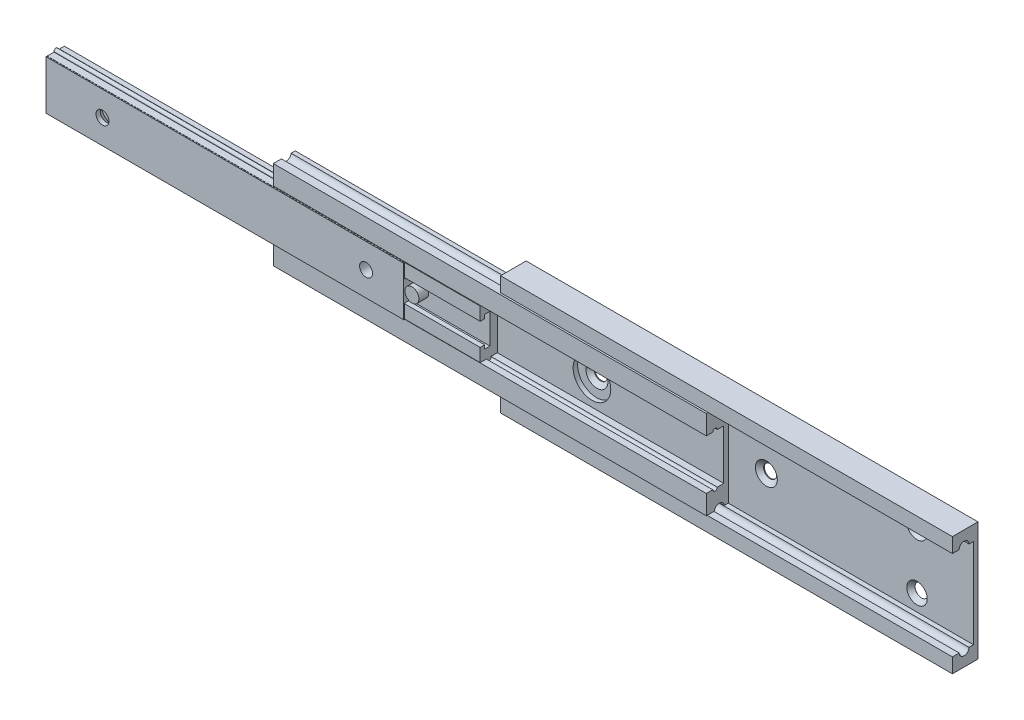
SolidWorks part; units mm, degrees
ref_plane "Front" through (0, 0, 0) normal (0, 0, 1) x (1, 0, 0)
ref_plane "Top" through (0, 0, 0) normal (0, 1, 0) x (1, 0, 0)
ref_plane "Right" through (0, 0, 0) normal (1, 0, 0) x (0, 0, -1)
sketch "Sketch1" plane through (0, 0, 0) normal (1, 0, 0) x (0, 0, -1)
  line L0 (-4.318, -20.0422) -> (4.318, 20.0422) construction
  line L1 (-4.318, 20.0422) -> (4.318, 20.0422)
  line L2 (-4.318, 20.0422) -> (-4.318, 15.0892)
  line L3 (-4.318, -20.0422) -> (4.318, -20.0422)
  line L4 (4.318, 20.0422) -> (4.318, -20.0422)
  line L5 (2.794, 15.0892) -> (2.794, -15.0892)
  line L6 (2.794, 15.0892) -> (1.27, 15.0892)
  line L7 (2.794, -15.0892) -> (1.27, -15.0892)
  line L8 (-4.318, -15.0892) -> (-4.318, -20.0422)
  line L9 (-2.032, 15.0892) -> (-4.318, 15.0892)
  line L10 (-2.032, -15.0892) -> (-4.318, -15.0892)
  arc A0 (1.27, 15.0892) -> (-2.032, 15.0892) centre (-0.381, 15.0892) ccw
  arc A1 (-2.032, -15.0892) -> (1.27, -15.0892) centre (-0.381, -15.0892) ccw
  dimension "D5" = 3.302
  dimension "D1" = 40.0844
  dimension "D2" = 8.636
  dimension "D3" = 1.524
  dimension "D4" = 4.953
  dimension "D6" = 3.175
extrude "Extrude1" add sketch "Sketch1" along normal blind 152.4
ref_plane "Plane1" through (-76.2, 0, 0) normal (1, 0, 0) x (0, 0, -1)
sketch "Sketch2" plane through (-76.2, 0, 0) normal (1, 0, 0) x (0, 0, -1)
  line L0 (2.794, 15.0892) -> (2.794, -15.0892) construction
  line L1 (-4.7625, 14.9368) -> (-2.025, 14.9368)
  line L2 (-4.7625, 14.9368) -> (-4.7625, 8.4074)
  line L3 (-4.7625, -14.9368) -> (-2.025, -14.9368)
  line L4 (2.6416, 14.9368) -> (2.6416, -14.9368)
  line L5 (-4.318, 15.0892) -> (-2.032, 15.0892) construction
  line L6 (4.318, -20.0422) -> (4.318, 20.0422) construction
  line L7 (-2.032, -15.0892) -> (-4.318, -15.0892) construction
  line L8 (1.263, -14.9368) -> (2.6416, -14.9368)
  line L9 (1.263, 14.9368) -> (2.6416, 14.9368)
  line L10 (-4.7625, 8.4074) -> (-2.5844, 8.4074)
  line L11 (-3.6068, 8.255) -> (0.9652, 8.255) construction
  line L12 (-3.6068, 8.255) -> (-3.6068, -8.255) construction
  line L13 (-3.6068, -8.255) -> (0.9652, -8.255) construction
  line L14 (0.9652, 8.255) -> (0.9652, -8.255) construction
  line L15 (1.1176, 8.4074) -> (1.1176, -8.4074)
  line L16 (1.1176, -8.4074) -> (-1.0604, -8.4074)
  line L17 (-4.7625, -8.4074) -> (-4.7625, -14.9368)
  line L18 (-1.0604, 8.4074) -> (1.1176, 8.4074)
  line L19 (-4.7625, 8.4074) -> (1.1176, 8.4074) construction
  line L20 (-2.5844, -8.4074) -> (-4.7625, -8.4074)
  arc A0 (-2.025, 14.9368) -> (1.263, 14.9368) centre (-0.381, 15.0892) ccw
  arc A1 (1.27, 15.0892) -> (-2.032, 15.0892) centre (-0.381, 15.0892) ccw construction
  arc A2 (1.263, -14.9368) -> (-2.025, -14.9368) centre (-0.381, -15.0892) ccw
  arc A3 (-2.032, -15.0892) -> (1.27, -15.0892) centre (-0.381, -15.0892) ccw construction
  arc A4 (-1.0604, 8.4074) -> (-2.5844, 8.4074) centre (-1.8224, 8.4074) ccw
  arc A5 (-2.5844, -8.4074) -> (-1.0604, -8.4074) centre (-1.8224, -8.4074) ccw
  point P28 (0.9652, 0)
  dimension "D11" = 1.524
  dimension "D1" = 0.1524
  dimension "D2" = 0.1524
  dimension "D3" = 9.0805
  dimension "D4" = 0.1524
  dimension "D5" = 16.51
  dimension "D6" = 7.9248
  dimension "D7" = 4.572
  dimension "D8" = 0.1524
  dimension "D9" = 0.1524
  dimension "D10" = 0.1524
extrude "Extrude2" add sketch "Sketch2" along normal blind 146.05
ref_plane "Plane2" through (-152.4, 0, 0) normal (1, 0, 0) x (0, 0, -1)
sketch "Sketch3" plane through (-152.4, 0, 0) normal (1, 0, 0) x (0, 0, -1)
  line L0 (4.318, -20.0422) -> (4.318, 20.0422) construction
  line L1 (-4.826, 8.255) -> (-2.5209, 8.255)
  line L2 (-4.826, 8.255) -> (-4.826, 3.81)
  line L3 (-4.826, -8.255) -> (-2.5209, -8.255)
  line L4 (0.9652, 8.255) -> (0.9652, -8.255)
  line L5 (-4.7625, 8.4074) -> (-2.5844, 8.4074) construction
  line L6 (1.1176, 8.4074) -> (1.1176, -8.4074) construction
  line L7 (-1.1239, 8.255) -> (0.9652, 8.255)
  line L8 (-2.5209, 8.4074) -> (-2.5209, 8.255)
  line L9 (-1.1239, 8.4074) -> (-1.1239, 8.255)
  line L10 (-2.5209, -8.4074) -> (-2.5209, -8.255)
  line L11 (-1.1239, -8.4074) -> (-1.1239, -8.255)
  line L12 (-1.1239, -8.255) -> (0.9652, -8.255)
  line L13 (-4.826, 8.255) -> (-4.7625, 8.4074) construction
  line L14 (-4.7625, -8.4074) -> (-4.826, -8.255) construction
  line L15 (-4.826, 3.81) -> (-3.302, 3.81)
  line L16 (-3.302, 3.81) -> (-3.302, 5.08)
  line L17 (-3.302, 5.08) -> (-1.524, 5.08)
  line L18 (-4.826, -3.81) -> (-4.826, -8.255)
  line L19 (-1.524, 5.08) -> (-1.524, -5.08)
  line L20 (-1.524, -5.08) -> (-3.302, -5.08)
  line L21 (-3.302, -5.08) -> (-3.302, -3.81)
  line L22 (-3.302, -3.81) -> (-4.826, -3.81)
  arc A0 (-1.1239, 8.4074) -> (-2.5209, 8.4074) centre (-1.8224, 8.4074) ccw
  arc A3 (-1.0604, 8.4074) -> (-2.5844, 8.4074) centre (-1.8224, 8.4074) ccw construction
  arc A4 (-2.5209, -8.4074) -> (-1.1239, -8.4074) centre (-1.8224, -8.4074) ccw
  arc A5 (-2.5844, -8.4074) -> (-1.0604, -8.4074) centre (-1.8224, -8.4074) ccw construction
  dimension "D5" = 1.397
  dimension "D1" = 7.62
  dimension "D2" = 9.144
  dimension "D3" = 0.1524
  dimension "D4" = 0.1524
  dimension "D6" = 10.16
  dimension "D7" = 1.778
  dimension "D8" = 1.524
extrude "Extrude3" add sketch "Sketch3" along normal blind 146.05
sketch "Sketch9" plane through (0, 0, 1.524) normal (0, 0, 1) x (1, 0, 0)
  line L0 (-6.35, 5.08) -> (-6.35, -5.08) construction
  circle A0 centre (-29.3751, 0) radius 2.3749
  dimension "D2" = 4.7498
  dimension "D1" = 25.4
extrude "Extrude4" add sketch "Sketch9" along normal up to surface (3.302 mm away) up to face at (-79.375, 6.0325, 4.826)
sketch "Sketch10" plane through (-152.4, 0, 0) normal (1, 0, 0) x (0, 0, -1)
  line L0 (-4.8768, 8.255) -> (-4.8768, 3.556)
  line L1 (-4.8768, 3.556) -> (-3.048, 3.556)
  line L2 (-3.048, 3.556) -> (-3.048, 4.826)
  line L3 (-3.048, 4.826) -> (-1.778, 4.826)
  line L4 (-1.778, 4.826) -> (-1.778, -4.826)
  line L5 (-1.778, -4.826) -> (-3.048, -4.826)
  line L6 (-3.048, -4.826) -> (-3.048, -3.556)
  line L7 (-3.048, -3.556) -> (-4.8768, -3.556)
  line L8 (-4.8768, -3.556) -> (-4.8768, -8.255)
  line L9 (-4.8768, -8.255) -> (-5.207, -8.255)
  line L10 (-5.207, -8.255) -> (-5.207, 8.255)
  line L11 (-5.207, 8.255) -> (-4.8768, 8.255)
  line L12 (-1.778, 0) -> (-5.207, 0) construction
  line L13 (4.318, -20.0422) -> (4.318, 20.0422) construction
  line L14 (-4.826, 8.255) -> (-4.826, 3.81) construction
  line L15 (-4.826, 3.81) -> (-3.302, 3.81) construction
  line L16 (-3.302, 3.81) -> (-3.302, 5.08) construction
  line L17 (-1.524, 5.08) -> (-1.524, -5.08) construction
  line L18 (-3.302, 5.08) -> (-1.524, 5.08) construction
  dimension "D1" = 16.51
  dimension "D2" = 9.525
  dimension "D3" = 0.0508
  dimension "D4" = 0.254
  dimension "D5" = 0.254
  dimension "D6" = 0.254
  dimension "D7" = 0.254
extrude "Extrude5" add sketch "Sketch10" along normal blind 120.65
sketch "Sketch4" plane through (0, 0, -2.794) normal (0, 0, 1) x (1, 0, 0)
  line L0 (152.4, 20.0422) -> (152.4, 15.0892) construction
  line L1 (152.4, 0) -> (14.7326, 0) construction
  line L2 (152.4, 15.0892) -> (152.4, -15.0892) construction
  circle A0 centre (133.35, 9.525) radius 2.1844
  circle A1 centre (133.35, -9.525) radius 2.1844
  circle A9 centre (82.55, 0) radius 2.1844
  circle A10 centre (25.4, 0) radius 2.1844
  dimension "D3" = 4.3688
  dimension "D4" = 19.05
  dimension "D5" = 50.8
  dimension "D10" = 107.95
  dimension "D1" = 19.05
extrude "Cut-Extrude1" cut sketch "Sketch4" against normal up to next (1.524 mm away)
chamfer "Chamfer1" distance 1.27 angle 50 4 edges at (135.5344, 9.525, -2.794) (135.5344, -9.525, -2.794) (27.5844, 0, -2.794) (84.7344, 0, -2.794)
sketch "Sketch5" plane through (0, 0, -1.1176) normal (0, 0, 1) x (1, 0, 0)
  circle A6 centre (25.4, 0) radius 6.35
  circle A7 centre (82.55, 0) radius 6.35
  circle A9 centre (82.55, 0) radius 2.1844 construction
  circle A10 centre (25.4, 0) radius 2.1844 construction
  dimension "D1" = 12.7
extrude "Cut-Extrude2" cut sketch "Sketch5" against normal up to next (1.524 mm away)
sketch "Sketch6" plane through (0, 0, 5.207) normal (0, 0, 1) x (1, 0, 0)
  line L0 (-249.6761, 0) -> (-31.75, 0) construction
  line L1 (-152.4, 8.255) -> (-152.4, 3.81) construction
  line L2 (-31.75, 8.255) -> (-31.75, -8.255) construction
  circle A0 centre (-133.35, 0) radius 2.1844
  circle A7 centre (-44.45, 0) radius 2.1844
  dimension "D1" = 4.3688
  dimension "D7" = 88.9
  dimension "D2" = 19.05
extrude "Cut-Extrude3" cut sketch "Sketch6" against normal up to next (3.429 mm away)
chamfer "Chamfer2" distance 1.6637 angle 50 1 edges at (-133.35, -2.1844, 1.778)
equation "\"D1@Extrude2\" = \"D1@Extrude1\"-.25"
equation "\"D1@Extrude3\"=\"D1@Extrude2\""
equation "\"D1@Extrude5\"=\"D1@Extrude3\"-1"
